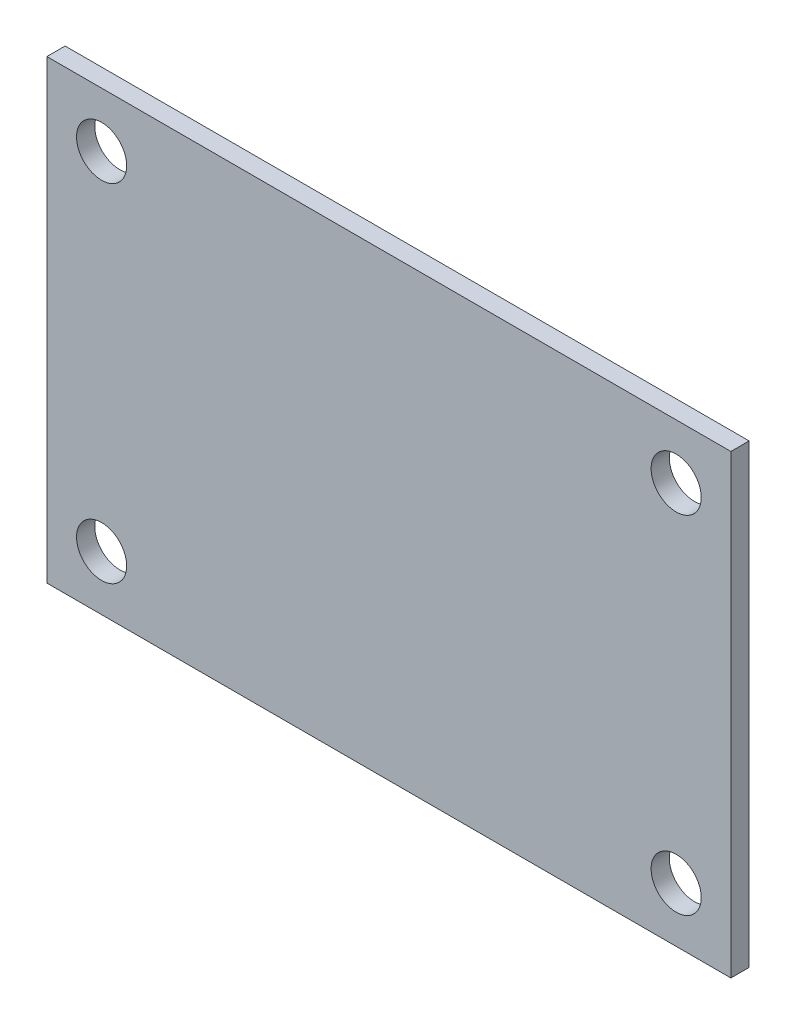
SolidWorks part; units mm, degrees
ref_plane "Płaszczyzna przednia" through (0, 0, 0) normal (0, 0, 1) x (1, 0, 0)
ref_plane "Płaszczyzna górna" through (0, 0, 0) normal (0, 1, 0) x (1, 0, 0)
ref_plane "Płaszczyzna prawa" through (0, 0, 0) normal (1, 0, 0) x (0, 0, -1)
sketch "Szkic1" plane through (0, 0, 0) normal (0, 0, 1) x (1, 0, 0)
  line L0 (55, 0) -> (-55, 0) construction
  line L1 (-75, 50) -> (75, 50)
  line L2 (-75, 50) -> (-75, -50)
  line L3 (-75, -50) -> (75, -50)
  line L4 (75, 50) -> (75, -50)
  line L5 (0, -55) -> (0, 55) construction
  point P4 (-75, 0)
  point P9 (0, -50)
  dimension "D1" = 100
  dimension "150" = 150
  dimension "D2" = 0
extrude "Dodanie-wyciągnięcie1" add sketch "Szkic1" along normal blind 4
hole_wizard "Otwór pod śrubę M101" positions "Szkic2" profile "Szkic3" hole size "M10" standard "ISO" end condition through all
sketch "Szkic2" plane through (0, 0, 4) normal (0, 0, 1) x (1, 0, 0)
  line L0 (-75, 50) -> (-75, -50) construction
  line L2 (75, 50) -> (-75, 50) construction
  point P0 (-63, 38)
  dimension "D1" = 12
  dimension "D2" = 12
sketch "Szkic3" plane through (-63, 38, 4) normal (1, 0, 0) x (0, -1, 0)
  line L0 (0, 0) -> (0, 4)
  line L1 (0, 4) -> (5.5, 4)
  line L2 (5.5, 4) -> (5.5, 0)
  line L5 (5.5, 0) -> (0, 0)
  line L11 (0, -6.35) -> (0, 107.95) construction
  dimension "Średnica otworu na wylot" = 11
  dimension "Głębokość otworu na wylot" = 4
mirror "Lustro1" about plane through (0, 0, 0) normal (0, 1, 0) of "Otwór pod śrubę M101" second plane through (0, 0, 0) second plane normal (1, 0, 0)
